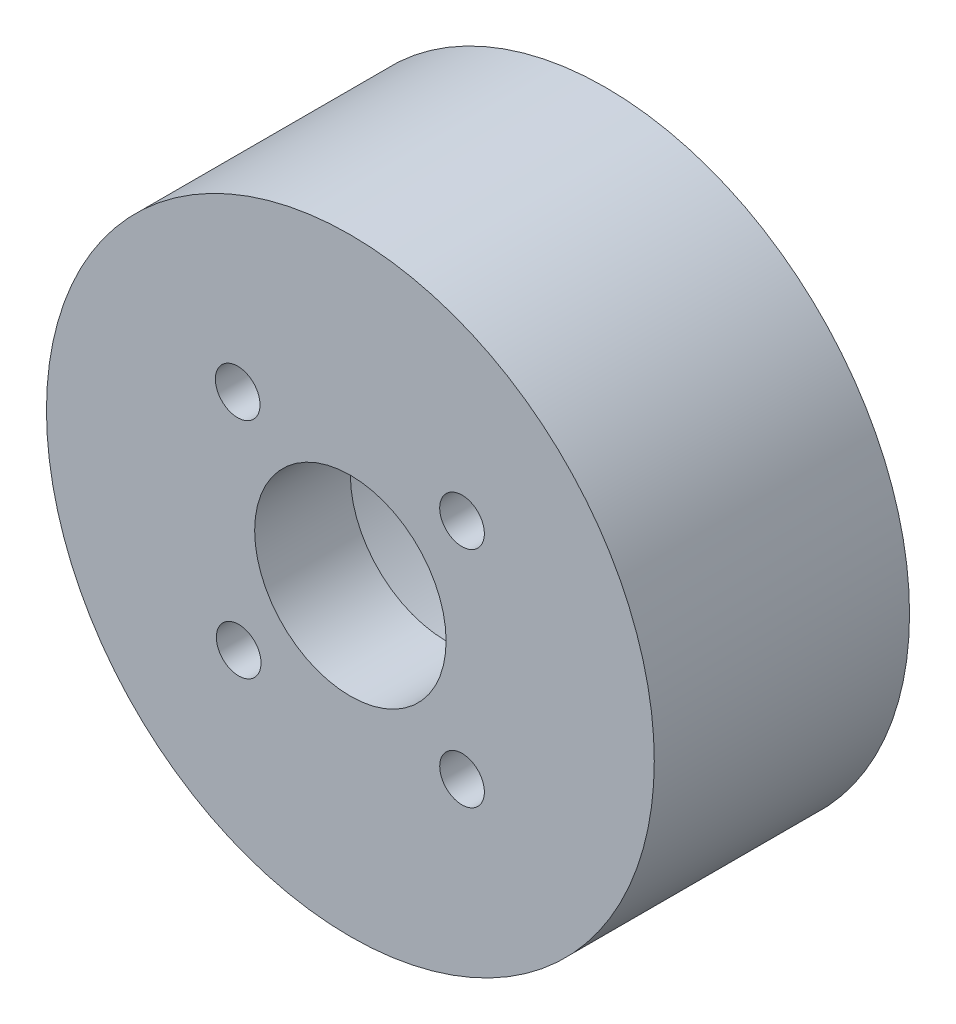
SolidWorks part; units mm, degrees
ref_plane "Front Plane" through (0, 0, 0) normal (0, 0, 1) x (1, 0, 0)
ref_plane "Top Plane" through (0, 0, 0) normal (0, 1, 0) x (1, 0, 0)
ref_plane "Right Plane" through (0, 0, 0) normal (1, 0, 0) x (0, 0, -1)
sketch "Sketch1" plane through (0, 0, 0) normal (0, 0, 1) x (1, 0, 0)
  circle A0 centre (0, 0) radius 19.05
  dimension "D1" = 38.1
extrude "Boss-Extrude1" add sketch "Sketch1" along normal blind 16
sketch "Sketch2" plane through (0, 0, 0) normal (0, 0, -1) x (-1, 0, 0)
  circle A0 centre (0, 0) radius 15.4
  dimension "D1" = 30.8
extrude "Cut-Extrude1" cut sketch "Sketch2" against normal blind 10
sketch "Sketch3" plane through (0, 0, 10) normal (0, 0, -1) x (-1, 0, 0)
  line L1 (-7, 7) -> (7, 7)
  line L2 (-7, 7) -> (-7, -7)
  line L3 (-7, -7) -> (7, -7)
  line L4 (7, 7) -> (7, -7)
  line L5 (-7, 7) -> (7, -7) construction
  line L6 (-7, -7) -> (7, 7) construction
  point P0 (0, 0)
  dimension "D1" = 14
  dimension "D2" = 14
sketch "Sketch4" plane through (0, 0, 10) normal (0, 0, -1) x (-1, 0, 0)
  circle A0 centre (-7, 7) radius 2.5
  circle A1 centre (7, 7) radius 2.5
  circle A2 centre (7, -7) radius 2.5
  circle A3 centre (-7, -7) radius 2.5
  dimension "D1" = 5
  dimension "D2" = 5
  dimension "D3" = 5
  dimension "D4" = 5
extrude "Cut-Extrude3" cut sketch "Sketch4" against normal blind 1.4
sketch "Sketch5" plane through (0, 0, 11.4) normal (0, 0, -1) x (-1, 0, 0)
  circle A0 centre (-6.998, 7.02) radius 1.4
  dimension "D1" = 2.8
extrude "Cut-Extrude4" cut sketch "Sketch5" against normal through all
sketch "Sketch6" plane through (0, 0, 11.4) normal (0, 0, -1) x (-1, 0, 0)
  circle A0 centre (7.0627, 6.9864) radius 1.4
  dimension "D1" = 2.8
extrude "Cut-Extrude5" cut sketch "Sketch6" against normal through all
sketch "Sketch9" plane through (0, 0, 11.4) normal (0, 0, -1) x (-1, 0, 0)
  circle A0 centre (-7, -7) radius 1.4
  dimension "D1" = 2.8
extrude "Cut-Extrude8" cut sketch "Sketch9" against normal through all
sketch "Sketch10" plane through (0, 0, 11.4) normal (0, 0, -1) x (-1, 0, 0)
  circle A0 centre (7, -7) radius 1.4
  dimension "D1" = 2.8
extrude "Cut-Extrude9" cut sketch "Sketch10" against normal through all
sketch "Sketch11" plane through (0, 0, 10) normal (0, 0, -1) x (-1, 0, 0)
  circle A0 centre (0, 0) radius 6
  dimension "D1" = 12
extrude "Cut-Extrude11" cut sketch "Sketch11" against normal through all
